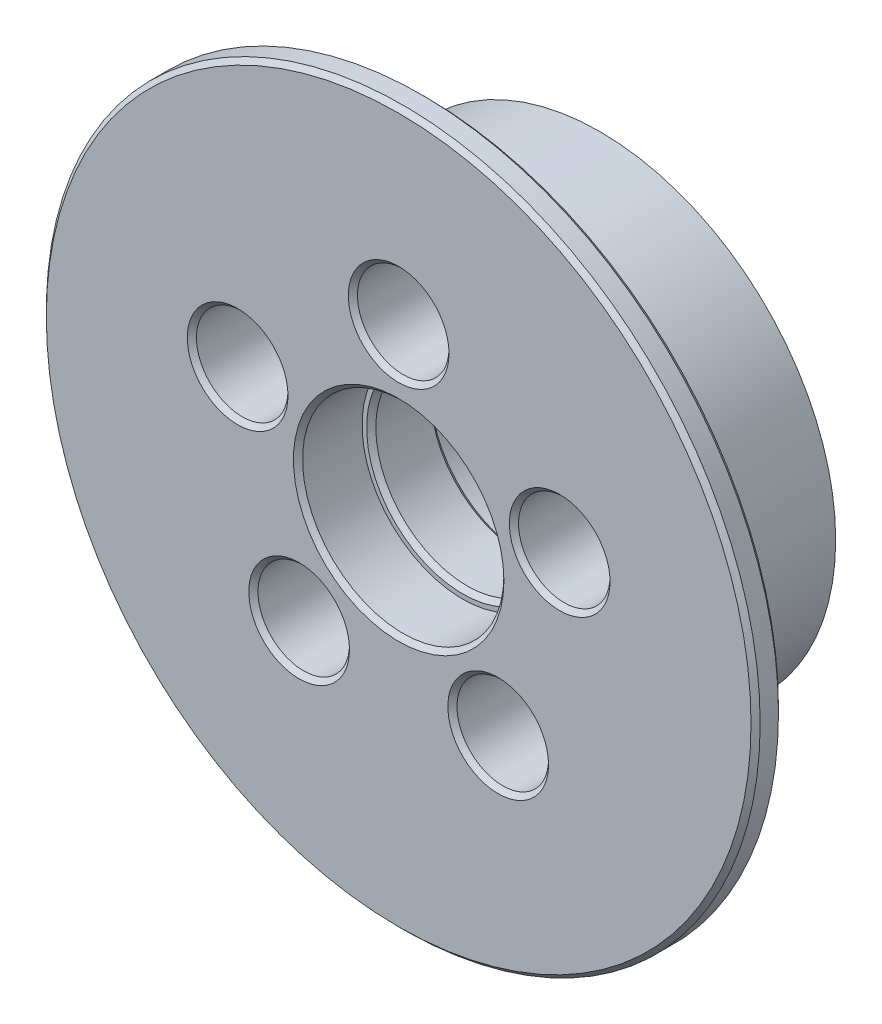
SolidWorks part; units mm, degrees
ref_plane "Front Plane" through (0, 0, 0) normal (0, 0, 1) x (1, 0, 0)
ref_plane "Top Plane" through (0, 0, 0) normal (0, 1, 0) x (1, 0, 0)
ref_plane "Right Plane" through (0, 0, 0) normal (1, 0, 0) x (0, 0, -1)
sketch "Sketch1" plane through (0, 0, 0) normal (0, 0, 1) x (1, 0, 0)
  circle A0 centre (0, 0) radius 25.75
  dimension "D1" = 51.5
extrude "Boss-Extrude1" add sketch "Sketch1" along normal blind 19
sketch "Sketch2" plane through (0, 0, 19) normal (0, 0, 1) x (1, 0, 0)
  circle A0 centre (0, 0) radius 39
  dimension "D1" = 78
extrude "Boss-Extrude2" add sketch "Sketch2" along normal blind 3
sketch "Sketch3" plane through (0, 0, 0) normal (0, 0, -1) x (-1, 0, 0)
  circle A0 centre (0, 0) radius 18.5 construction
  circle A1 centre (0, 18.5) radius 5
  circle A2 centre (17.5945, 5.7168) radius 5
  circle A3 centre (10.874, -14.9668) radius 5
  circle A4 centre (-10.874, -14.9668) radius 5
  circle A5 centre (-17.5945, 5.7168) radius 5
  point P16 (0, 0)
  dimension "D2" = 10
  dimension "D3" = 37
  dimension "D1" = 5
extrude "Cut-Extrude1" cut sketch "Sketch3" against normal through all
sketch "Sketch4" plane through (0, 0, 0) normal (0, 0, -1) x (-1, 0, 0)
  circle A0 centre (0, 0) radius 10
  dimension "D1" = 20
extrude "Cut-Extrude2" cut sketch "Sketch4" against normal through all
sketch "Sketch5" plane through (0, 0, 0) normal (0, 0, -1) x (-1, 0, 0)
  circle A0 centre (0, 0) radius 11
  circle A3 centre (0, 0) radius 10 construction
  dimension "D1" = 1
extrude "Cut-Extrude3" cut sketch "Sketch5" against normal blind 8
sketch "Sketch6" plane through (0, 0, 22) normal (0, 0, 1) x (1, 0, 0)
  circle A0 centre (0, 0) radius 11
  circle A3 centre (0, 0) radius 10 construction
  dimension "D1" = 1
extrude "Cut-Extrude4" cut sketch "Sketch6" against normal blind 7
chamfer "Chamfer1" distance 0.5 angle 45 11 edges at (11, 0, 22) (-15.874, -14.9668, 22) (5.874, -14.9668, 22) (12.5945, 5.7168, 22) (-5, 18.5, 22) (-22.5945, 5.7168, 22) (-11, 0, 0) (-10, 0, 8) (10, 0, 15) (39, 0, 22) (39, 0, 19)
fillet "Fillet1" radius 1 5 edges at (-5, 18.5, 0) (-22.5945, 5.7168, 0) (-15.874, -14.9668, 0) (5.874, -14.9668, 0) (12.5945, 5.7168, 0)
